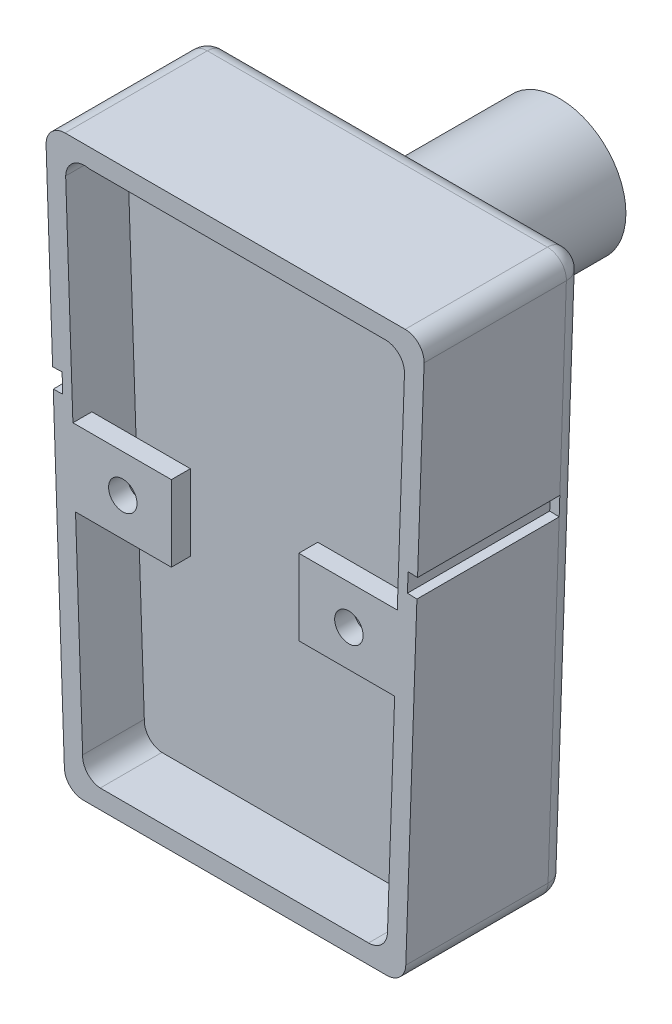
SolidWorks part; units mm, degrees
ref_plane "Front Plane" through (0, 0, 0) normal (0, 0, 1) x (1, 0, 0)
ref_plane "Top Plane" through (0, 0, 0) normal (0, 1, 0) x (1, 0, 0)
ref_plane "Right Plane" through (0, 0, 0) normal (1, 0, 0) x (0, 0, -1)
sketch "Sketch3" plane through (0, 0, 0) normal (0, 0, 1) x (1, 0, 0)
  line L0 (-22.7709, 76.1547) -> (22.7709, 76.1547)
  line L1 (25.3094, 73.5272) -> (22.8585, 2.4525)
  line L2 (20.32, 0) -> (-20.32, 0)
  line L3 (0, 76.1547) -> (0, 0) construction
  line L4 (-25.3094, 73.5272) -> (-22.8585, 2.4525)
  line L5 (-19.5413, 73.6147) -> (20.1418, 73.6147)
  line L6 (22.6803, 70.9872) -> (20.4046, 4.9925)
  line L7 (17.8661, 2.54) -> (-18.0612, 2.54)
  line L8 (-22.688, 71.2103) -> (-20.4122, 5.2126)
  arc A0 (22.8585, 2.4525) -> (20.32, 0) centre (20.32, 2.54) cw
  arc A1 (22.7709, 76.1547) -> (25.3094, 73.5272) centre (22.7709, 73.6147) cw
  arc A2 (-22.8585, 2.4525) -> (-20.32, 0) centre (-20.32, 2.54) ccw
  arc A3 (-22.7709, 76.1547) -> (-25.3094, 73.5272) centre (-22.7709, 73.6147) ccw
  arc A4 (20.4046, 4.9925) -> (17.8661, 2.54) centre (17.8661, 5.08) cw
  arc A5 (20.1418, 73.6147) -> (22.6803, 70.9872) centre (20.1418, 71.0747) cw
  arc A6 (-20.4122, 5.2126) -> (-18.0612, 2.54) centre (-17.876, 5.0732) ccw
  arc A7 (-19.5413, 73.6147) -> (-22.688, 71.2103) centre (-20.1487, 71.1484) ccw
  point P26 (-21.6909, 73.1667)
  dimension "D7" = 2.54
  dimension "D8" = 2.54
  dimension "D9" = 2.54
  dimension "D10" = 40.64
  dimension "D18" = 17.876
  dimension "D1" = 45.5418
  dimension "D2" = 2.54
  dimension "D3" = 39.6831
  dimension "D4" = 71.0747
  dimension "D5" = 65.9947
  dimension "D6" = 2.54
  dimension "D11" = 35.9272
  dimension "D12" = 65.9978
  dimension "D13" = 1.975
  dimension "D14" = 0
  dimension "D15" = 0
  dimension "D16" = 20.2204
  dimension "D17" = 21.6909
extrude "Boss-Extrude2" add sketch "Sketch3" along normal blind 21.59 contours L5 L3 L7 A4 L6 A5 | L3 L5 A7 L8 A6 L7 | L0 L3 L5 A5 L6 A4 L7 L2 A0 L1 A1 | L3 L0 A3 L4 A2 L2 L7 A6 L8 A7 L5
sketch "Sketch4" plane through (0, 0, 21.59) normal (0, 0, 1) x (1, 0, 0)
  line L3 (0, 76.1547) -> (0, 0) construction
  line L5 (-19.5413, 73.6147) -> (20.1418, 73.6147)
  line L6 (22.6803, 70.9872) -> (20.4046, 4.9925)
  line L7 (17.8661, 2.54) -> (-18.0612, 2.54)
  line L8 (-22.688, 71.2103) -> (-20.4122, 5.2126)
  line L9 (-22.7709, 76.1547) -> (22.7709, 76.1547) construction
  line L10 (25.3094, 73.5272) -> (22.8585, 2.4525) construction
  arc A4 (20.4046, 4.9925) -> (17.8661, 2.54) centre (17.8661, 5.08) cw
  arc A5 (20.1418, 73.6147) -> (22.6803, 70.9872) centre (20.1418, 71.0747) cw
  arc A6 (-20.4122, 5.2126) -> (-18.0612, 2.54) centre (-17.876, 5.0732) ccw
  arc A7 (-19.5413, 73.6147) -> (-22.688, 71.2103) centre (-20.1487, 71.1484) ccw
  point P6 (0, 0)
  point P26 (-21.6909, 73.1667)
  dimension "D7" = 1.975
  dimension "D8" = 2.54
  dimension "D9" = 2.54
  dimension "D18" = 17.876
  dimension "D2" = 2.54
  dimension "D3" = 39.6831
  dimension "D4" = 2.54
  dimension "D5" = 65.9947
  dimension "D6" = 2.54
  dimension "D11" = 35.9272
  dimension "D12" = 65.9978
  dimension "D14" = 0
  dimension "D16" = 20.2204
  dimension "D17" = 21.6909
extrude "Cut-Extrude1" cut sketch "Sketch4" against normal blind 17.78
sketch "Sketch7" plane through (0, 0, 21.59) normal (0, 0, 1) x (1, 0, 0)
  line L0 (-24.0839, 37.9898) -> (24.0839, 37.9898) construction
  line L3 (-21.3673, 32.9098) -> (-21.7176, 43.0698) construction
  line L5 (-21.7176, 43.0698) -> (-8.5315, 43.0698)
  line L6 (-8.5315, 43.0698) -> (-8.5315, 32.9098)
  line L7 (-8.5315, 32.9098) -> (-21.3673, 32.9098)
  line L8 (20.1418, 73.6147) -> (-19.5413, 73.6147) construction
  line L9 (0, 76.1547) -> (0, 0) construction
  line L12 (8.5315, 32.9098) -> (21.3673, 32.9098)
  line L13 (8.5315, 43.0698) -> (8.5315, 32.9098)
  line L14 (21.7176, 43.0698) -> (8.5315, 43.0698)
  line L15 (-21.3673, 32.9098) -> (-21.7176, 43.0698)
  line L16 (21.3673, 32.9098) -> (21.7176, 43.0698)
  line L17 (-25.3094, 73.5272) -> (-22.8585, 2.4525) construction
  dimension "D1" = 5.08
  dimension "D2" = 5.08
  dimension "D3" = 17.0629
  dimension "D4" = 13.1861
  dimension "D5" = 30.5449
  dimension "D6" = 2.54
extrude "Boss-Extrude4" add sketch "Sketch7" against normal blind 2.54
sketch "Sketch8" plane through (0, 0, 21.59) normal (0, 0, 1) x (1, 0, 0)
  line L0 (-15.1245, 43.0698) -> (-14.9494, 32.9098) construction
  line L1 (-8.5315, 43.0698) -> (-21.7176, 43.0698) construction
  line L2 (-21.3673, 32.9098) -> (-8.5315, 32.9098) construction
  line L3 (0.3003, 73.6147) -> (-0.0975, 2.54) construction
  line L4 (20.1418, 73.6147) -> (-19.5413, 73.6147) construction
  line L5 (-18.0612, 2.54) -> (17.8661, 2.54) construction
  circle A0 centre (-15.0369, 37.9898) radius 1.905
  circle A1 centre (15.2377, 37.8204) radius 1.905
  dimension "D1" = 3.81
extrude "Cut-Extrude2" cut sketch "Sketch8" against normal blind 2.54
ref_plane "Plane4" through (0, 0, 10.795) normal (0, 0, 1) x (1, 0, 0)
sketch "Sketch10" plane through (0, 0, 10.795) normal (0, 0, 1) x (1, 0, 0)
  line L3 (0, 76.1547) -> (0, 0) construction
  line L5 (-19.4863, 73.6147) -> (20.1967, 73.6147)
  line L6 (22.7352, 70.9872) -> (20.4595, 4.9925)
  line L7 (17.921, 2.54) -> (-18.0062, 2.54)
  line L8 (-22.7445, 71.2567) -> (-20.4687, 5.2589)
  line L9 (-22.7709, 76.1547) -> (22.7709, 76.1547) construction
  arc A4 (20.4595, 4.9925) -> (17.921, 2.54) centre (17.921, 5.08) cw
  arc A5 (20.1967, 73.6147) -> (22.7352, 70.9872) centre (20.1967, 71.0747) cw
  arc A6 (-20.4687, 5.2589) -> (-18.0062, 2.54) centre (-17.9305, 5.0831) ccw
  arc A7 (-19.4863, 73.6147) -> (-22.7445, 71.2567) centre (-20.2057, 71.1787) ccw
  dimension "D7" = 17.9305
  dimension "D8" = 2.54
  dimension "D9" = 2.54
  dimension "D10" = 20.2057
  dimension "D2" = 1.975
  dimension "D3" = 39.6831
  dimension "D4" = 1.975
  dimension "D5" = 65.9947
  dimension "D6" = 2.54
  dimension "D11" = 35.9272
  dimension "D12" = 65.9978
  dimension "D13" = 20.2753
  dimension "D14" = 20.2753
extrude "Boss-Extrude6" add sketch "Sketch10" along normal blind 2.54
fillet "Fillet1" radius 2.54 8 edges at (-24.5976, 75.3796, 0) (-24.0839, 37.9898, 0) (-22.0848, 0.7133, 0) (22.0848, 0.7133, 0) (24.0839, 37.9898, 0) (24.5976, 75.3796, 0) (0, 0, 0) (0, 76.1547, 0)
sketch "Sketch13" plane through (22.7469, -0.7844, 0) normal (0.9994, -0.0345, 0) x (0, 0, -1)
  line L0 (-21.59, 47.7456) -> (-2.54, 47.7456) construction
  line L1 (-21.59, 74.3558) -> (-21.59, 3.2388) construction
  line L2 (-2.54, 3.2388) -> (-2.54, 74.3558) construction
  line L3 (-21.59, 74.3558) -> (-2.54, 74.3558) construction
  line L4 (-21.59, 49.0156) -> (-2.54, 49.0156)
  line L5 (-2.54, 49.0156) -> (-2.54, 46.4756)
  line L6 (-2.54, 46.4756) -> (-21.59, 46.4756)
  line L7 (-21.59, 46.4756) -> (-21.59, 49.0156)
  point P10 (-12.065, 47.7456)
  dimension "D1" = 26.6102
  dimension "D2" = 1.27
  dimension "D3" = 1.27
extrude "Cut-Extrude5" cut sketch "Sketch13" against normal blind 1.27
sketch "Sketch14" plane through (0, 0, 0) normal (0, 0, -1) x (-1, 0, 0)
  line L0 (-21.8533, 47.0045) -> (21.8533, 47.0045) construction
  line L1 (-22.7709, 73.6147) -> (-20.32, 2.54) construction
  line L2 (20.32, 2.54) -> (22.7709, 73.6147) construction
  line L3 (22.7709, 73.6147) -> (-22.7709, 73.6147) construction
  line L4 (-21.8971, 48.2745) -> (21.8533, 48.2745)
  line L5 (21.8533, 48.2745) -> (21.8533, 45.7345)
  line L6 (21.8533, 45.7345) -> (-21.8095, 45.7345)
  line L7 (-21.8095, 45.7345) -> (-21.8971, 48.2745)
  dimension "D1" = 26.6102
  dimension "D2" = 1.27
  dimension "D3" = 1.27
extrude "Cut-Extrude6" cut sketch "Sketch14" against normal blind 1.27
sketch "Sketch16" plane through (-22.7469, -0.7844, 0) normal (-0.9994, -0.0345, 0) x (0, 0, 1)
  line L0 (2.54, 47.7456) -> (21.59, 47.7456) construction
  line L1 (2.54, 74.3558) -> (2.54, 3.2388) construction
  line L2 (21.59, 74.3558) -> (21.59, 3.2388) construction
  line L3 (21.59, 74.3558) -> (2.54, 74.3558) construction
  line L4 (2.54, 49.0156) -> (21.59, 49.0156)
  line L5 (21.59, 49.0156) -> (21.59, 46.4756)
  line L6 (21.59, 46.4756) -> (2.54, 46.4756)
  line L7 (2.54, 46.4756) -> (2.54, 49.0156)
  dimension "D1" = 26.6102
  dimension "D2" = 1.27
  dimension "D3" = 1.27
extrude "Cut-Extrude7" cut sketch "Sketch16" against normal blind 1.27
sketch "Sketch17" plane through (0, 0, 0) normal (0, 0, -1) x (-1, 0, 0)
  line L0 (0, 73.6147) -> (-0.0219, 48.2745) construction
  line L1 (22.7709, 73.6147) -> (-22.7709, 73.6147) construction
  line L2 (21.8533, 48.2745) -> (-21.8971, 48.2745) construction
  circle A0 centre (-0.0109, 60.9446) radius 8.89
  dimension "D1" = 17.78
extrude "Boss-Extrude7" add sketch "Sketch17" along normal blind 21.844
fillet "Fillet2" radius 2.54 1 edges at (8.9009, 60.9446, 0)
